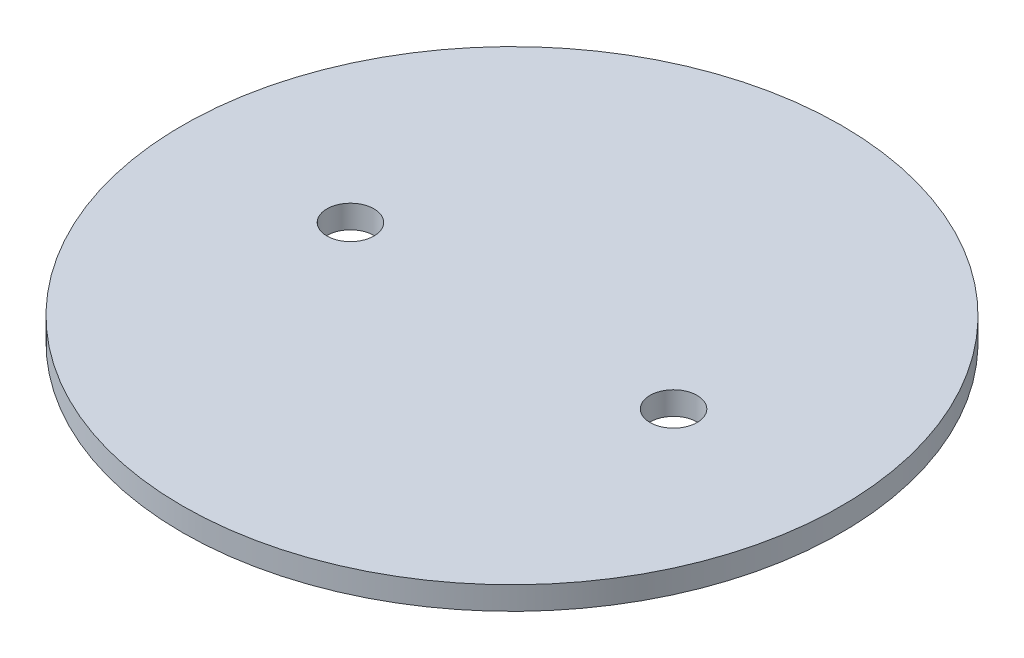
SolidWorks part; units mm, degrees
ref_plane "Front Plane" through (0, 0, 0) normal (0, 0, 1) x (1, 0, 0)
ref_plane "Top Plane" through (0, 0, 0) normal (0, 1, 0) x (1, 0, 0)
ref_plane "Right Plane" through (0, 0, 0) normal (1, 0, 0) x (0, 0, -1)
sketch "Sketch1" plane through (0, 0, 0) normal (0, 1, 0) x (1, 0, 0)
  line L0 (-22.225, 0) -> (22.225, 0) construction
  circle A0 centre (0, 0) radius 45.339
  circle A1 centre (22.225, 0) radius 3.2385
  circle A2 centre (-22.225, 0) radius 3.2385
  point P6 (0, 0)
  point P11 (0, 0)
  dimension "D1" = 6.477
  dimension "D2" = 90.678
  dimension "D3" = 44.45
extrude "Boss-Extrude1" add sketch "Sketch1" along normal blind 3.175
